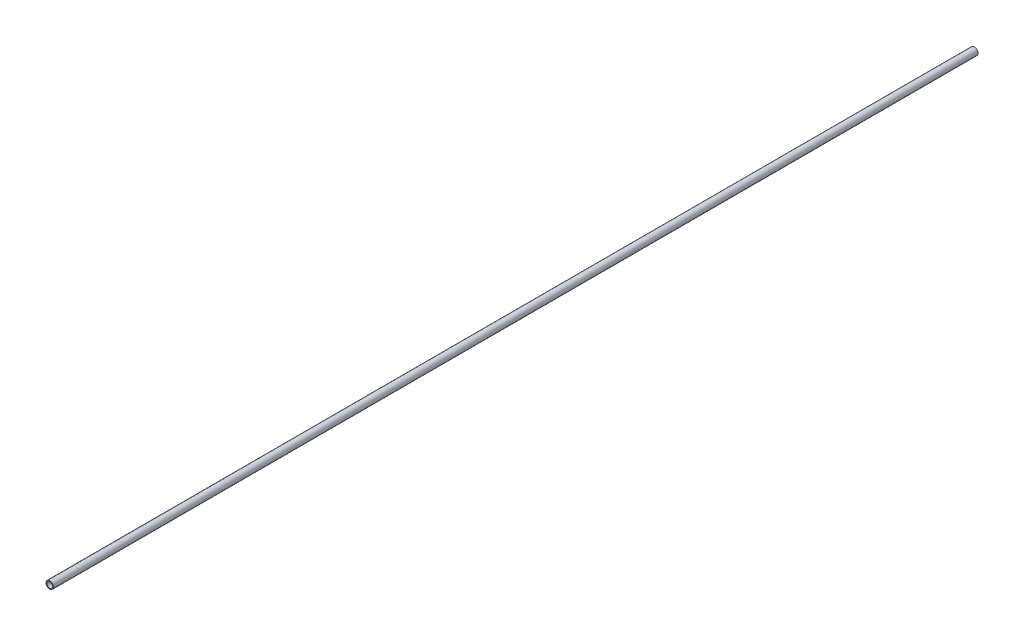
SolidWorks part; units mm, degrees
material "Poltrusion Carbon Fiber"
ref_plane "Front Plane" through (0, 0, 0) normal (0, 0, 1) x (1, 0, 0)
ref_plane "Top Plane" through (0, 0, 0) normal (0, 1, 0) x (1, 0, 0)
ref_plane "Right Plane" through (0, 0, 0) normal (1, 0, 0) x (0, 0, -1)
sketch "Эскиз1" plane through (0, 0, 0) normal (0, 0, 1) x (1, 0, 0)
  circle A0 centre (0, 0) radius 4
  circle A1 centre (0, 0) radius 3
  dimension "D1" = 8
  dimension "D2" = 6
extrude "Бобышка-Вытянуть1" add sketch "Эскиз1" along normal mid plane 1000
